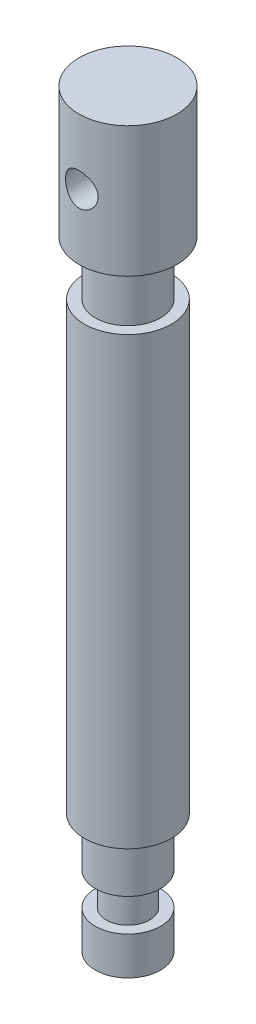
SolidWorks part; units mm, degrees
ref_plane "Front Plane" through (0, 0, 0) normal (0, 0, 1) x (1, 0, 0)
ref_plane "Top Plane" through (0, 0, 0) normal (0, 1, 0) x (1, 0, 0)
ref_plane "Right Plane" through (0, 0, 0) normal (1, 0, 0) x (0, 0, -1)
sketch "Sketch2" plane through (0, 0, 0) normal (0, 0, 1) x (1, 0, 0)
  line L0 (0, 0) -> (6, 0)
  line L1 (6, 0) -> (6, 7)
  line L2 (6, 7) -> (4, 7)
  line L3 (4, 7) -> (4, 13)
  line L4 (4, 13) -> (6, 13)
  line L5 (6, 13) -> (6, 22)
  line L6 (6, 22) -> (8, 22)
  line L7 (8, 22) -> (8, 104)
  line L8 (8, 104) -> (6, 104)
  line L9 (6, 104) -> (6, 114)
  line L10 (6, 114) -> (9, 114)
  line L11 (9, 114) -> (9, 138)
  line L12 (9, 138) -> (0, 138)
  line L13 (0, 138) -> (0, 0)
  dimension "D1" = 6
  dimension "D2" = 4
  dimension "D3" = 6
  dimension "D4" = 8
  dimension "D5" = 6
  dimension "D6" = 9
  dimension "D7" = 138
  dimension "D8" = 7
  dimension "D9" = 6
  dimension "D10" = 24
  dimension "D11" = 10
  dimension "D12" = 82
revolve "Revolve1" add sketch "Sketch2" angle 360 about L13
sketch "Sketch3" plane through (0, 0, 0) normal (0, 0, 1) x (1, 0, 0)
  line L0 (9, 138) -> (-9, 138) construction
  line L1 (0, 138) -> (0, 114) construction
  line L2 (-6, 114) -> (6, 114) construction
  circle A0 centre (0, 126) radius 3
  dimension "D1" = 6
  dimension "D2" = 12
extrude "Cut-Extrude1" cut sketch "Sketch3" against normal through all both and the other way through all
